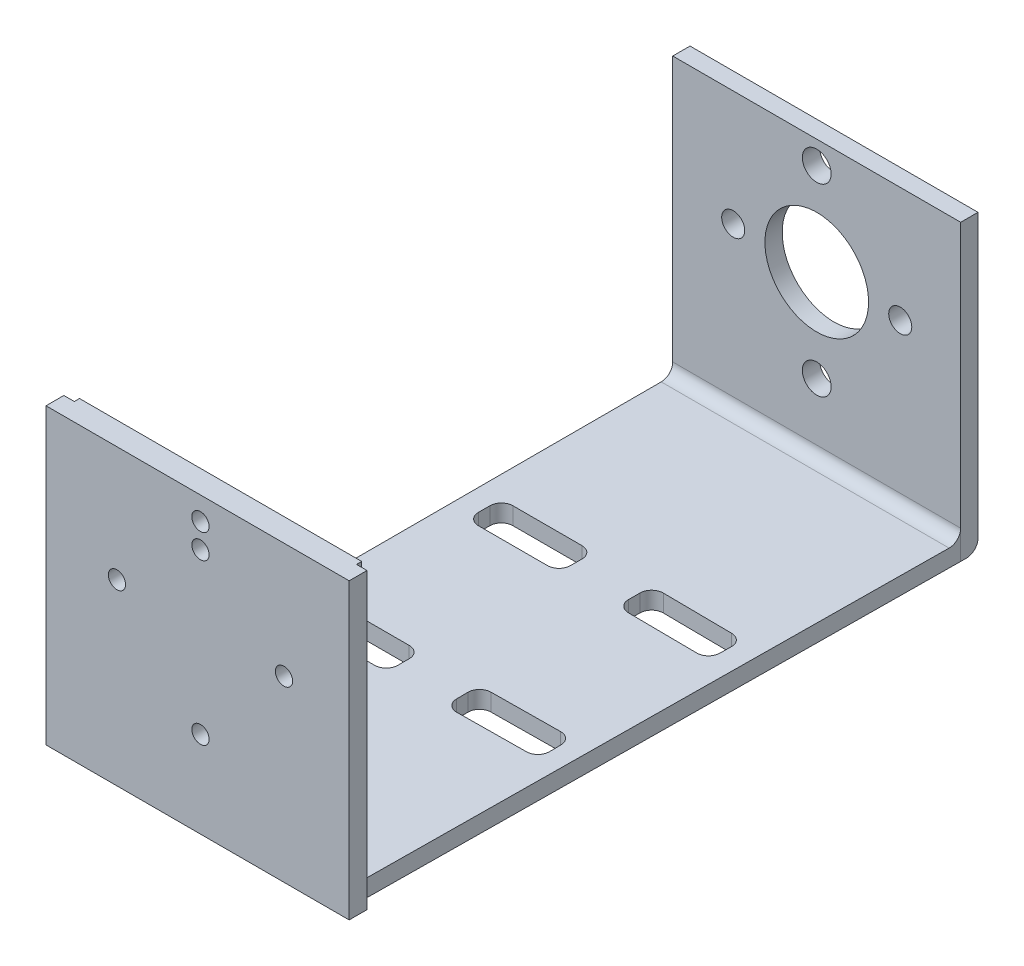
SolidWorks part; units mm, degrees
ref_plane "前视基准面" through (0, 0, 0) normal (0, 0, 1) x (1, 0, 0)
ref_plane "上视基准面" through (0, 0, 0) normal (0, 1, 0) x (1, 0, 0)
ref_plane "右视基准面" through (0, 0, 0) normal (1, 0, 0) x (0, 0, -1)
sketch "草图1" plane through (0, 0, 0) normal (0, 0, 1) x (1, 0, 0)
  line L0 (-25, 0) -> (-9, 0) construction
  line L2 (-25, 20) -> (-25, -31)
  line L3 (-25, -31) -> (25, -31)
  line L4 (25, 20) -> (25, -31)
  line L5 (-25, 31) -> (25, -31) construction
  line L6 (-25, -31) -> (23.9838, 29.7399) construction
  line L7 (-9, 0) -> (0, 0) construction
  line L8 (0, 0) -> (9, 0) construction
  line L9 (9, 0) -> (25, 0) construction
  line L10 (0, 31) -> (0, 0) construction
  line L11 (0, 0) -> (0, -9) construction
  line L12 (0, -9) -> (0, -31) construction
  line L13 (-25, 20) -> (25, 20)
  circle A0 centre (0, 0) radius 9
  circle A1 centre (14.5, 0) radius 2
  circle A2 centre (-14.5, 0) radius 2
  circle A3 centre (0, 16) radius 2.5
  circle A4 centre (0, -16) radius 2.5
  point P0 (0, 0)
  dimension "D3" = 18
  dimension "D5" = 4
  dimension "D6" = 4
  dimension "D8" = 5
  dimension "D1" = 49
  dimension "D2" = 62
  dimension "D4" = 29
  dimension "D7" = 14.5
  dimension "D9" = 16
  dimension "D10" = 51
extrude "凸台-拉伸1" add sketch "草图1" along normal blind 3
sketch "草图2" plane through (0, -31, 0) normal (0, -1, 0) x (1, 0, 0)
  line L0 (-25, 3) -> (-25, 106)
  line L1 (-25, 106) -> (24, 106)
  line L2 (24, 106) -> (25, 3)
  line L3 (-0.5, 106) -> (0, 3) construction
  line L4 (-25, 54.5) -> (-0.25, 54.5) construction
  line L5 (-0.25, 54.5) -> (24.5, 54.5) construction
  line L6 (-25, 3) -> (25, 3) construction
  line L7 (-25, 3) -> (25, 3)
  line L8 (-21.25, 42.5) -> (-5.25, 42.5)
  line L9 (-21.25, 42.5) -> (-21.25, 36.5)
  line L10 (-21.25, 36.5) -> (-5.25, 36.5)
  line L11 (-5.25, 42.5) -> (-5.25, 36.5)
  line L12 (-21.25, 42.5) -> (-5.25, 36.5) construction
  line L13 (-21.25, 36.5) -> (-5.25, 42.5) construction
  line L14 (4.8663, 42.5491) -> (4.9245, 36.5494)
  line L15 (20.9238, 36.7047) -> (4.9245, 36.5494)
  line L16 (20.8655, 42.7044) -> (20.9238, 36.7047)
  line L17 (20.8655, 42.7044) -> (4.8663, 42.5491)
  line L18 (-21.25, 66.5) -> (-21.25, 72.5)
  line L19 (-5.25, 66.5) -> (-5.25, 72.5)
  line L20 (-21.25, 72.5) -> (-5.25, 72.5)
  line L21 (-21.25, 66.5) -> (-5.25, 66.5)
  line L22 (20.8655, 66.2956) -> (20.9238, 72.2953)
  line L23 (20.9238, 72.2953) -> (4.9245, 72.4506)
  line L24 (4.8663, 66.4509) -> (4.9245, 72.4506)
  line L25 (20.8655, 66.2956) -> (4.8663, 66.4509)
  point P20 (-13.25, 39.5)
  dimension "D1" = 103
  dimension "D2" = 49
  dimension "D3" = 16
  dimension "D4" = 6
  dimension "D5" = 15
  dimension "D6" = 13
extrude "凸台-拉伸2" add sketch "草图2" against normal blind 3
sketch "草图3" plane through (0, 0, 106) normal (0, 0, 1) x (1, 0, 0)
  line L0 (24, 20) -> (-25, 20)
  line L1 (-25, -31) -> (24, -31)
  line L2 (-25, -31) -> (-25, 20)
  line L4 (24, -31) -> (24, 20)
  line L5 (24, -28) -> (-25, -28) construction
  circle A1 centre (-14.5, 0) radius 1.5
  circle A2 centre (14.5, 0) radius 1.5
  circle A3 centre (0, -16) radius 1.5
  circle A4 centre (0, 16) radius 1.5
  circle A5 centre (0, 11.75) radius 1.5
  dimension "D1" = 3
  dimension "D2" = 3
  dimension "D3" = 3
  dimension "D4" = 3
  dimension "D5" = 4.25
  dimension "D7" = 3
  dimension "D6" = 48
  dimension "D8" = 49
extrude "凸台-拉伸3" add sketch "草图3" along normal blind 4
fillet "圆角2" radius 2 1 edges at (-5.25, -29.5, 36.5)
fillet "圆角3" radius 2 3 edges at (-21.25, -29.5, 42.5) (-21.25, -29.5, 36.5) (-5.25, -29.5, 42.5)
fillet "圆角4" radius 2 12 edges at (-21.25, -29.5, 66.5) (-21.25, -29.5, 72.5) (-5.25, -29.5, 66.5) (-5.25, -29.5, 72.5) (4.9245, -29.5, 72.4506) (4.8663, -29.5, 66.4509) (20.9238, -29.5, 72.2953) (20.8655, -29.5, 66.2956) (4.8663, -29.5, 42.5491) (20.8655, -29.5, 42.7044) (20.9238, -29.5, 36.7047) (4.9245, -29.5, 36.5494)
fillet "圆角5" radius 2 1 edges at (0, -28, 3)
fillet "圆角6" radius 2 1 edges at (0, -31, 0)
ref_plane "基准面1" through (0, -31, 0) normal (0, -1, 0) x (-1, 0, 0)
sketch "草图4" plane through (0, -31, 0) normal (0, -1, 0) x (-1, 0, 0)
  line L1 (-24, -106.9) -> (-24, -110)
  line L2 (-24, -110) -> (-24, -106) construction
  line L4 (25, -110) -> (-24, -110) construction
  line L5 (0.5, -110) -> (0.5, -79.4929) construction
  line L13 (-24, -106.9) -> (-25.8187, -106.9)
  line L14 (-25.8187, -106.9) -> (-25.8187, -110)
  line L15 (-25.8187, -110) -> (-24, -110)
  line L16 (25, -106.9) -> (25, -110)
  line L17 (26.8187, -110) -> (25, -110)
  line L18 (26.8187, -106.9) -> (26.8187, -110)
  line L19 (25, -106.9) -> (26.8187, -106.9)
  point P1 (-24, -108.45)
  point P4 (25, -108.45)
  point P14 (0, 0)
  dimension "D2" = 1.8187
extrude "凸台-拉伸4" add sketch "草图4" against normal blind 51
